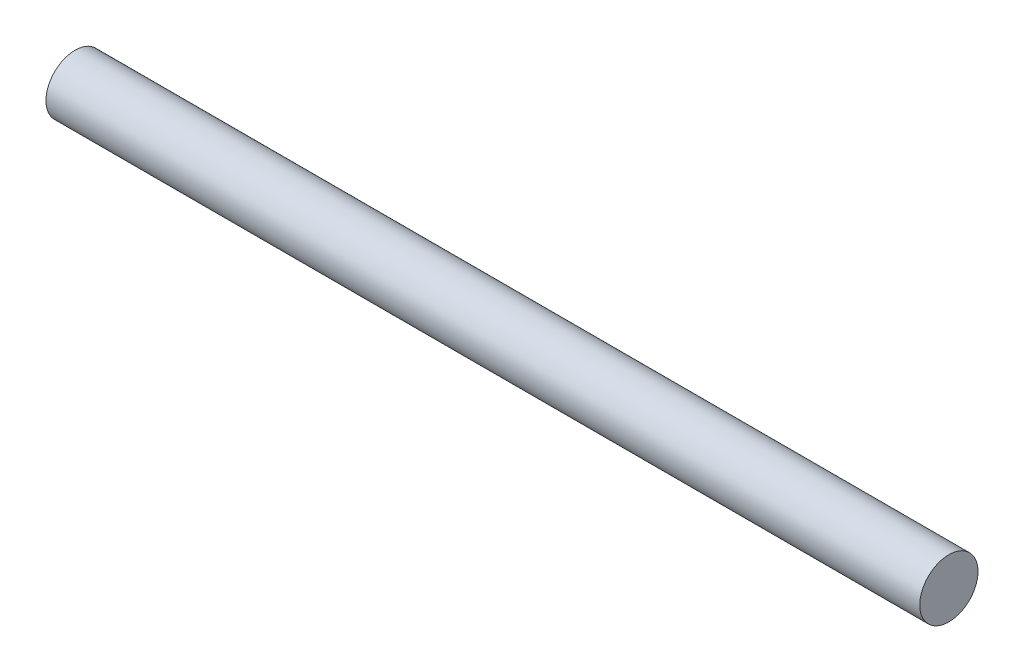
SolidWorks part; units mm, degrees
ref_plane "Alzado" through (0, 0, 0) normal (0, 0, 1) x (1, 0, 0)
ref_plane "Planta" through (0, 0, 0) normal (0, 1, 0) x (1, 0, 0)
ref_plane "Vista lateral" through (0, 0, 0) normal (1, 0, 0) x (0, 0, -1)
sketch "Croquis1" plane through (0, 0, 0) normal (1, 0, 0) x (0, 0, -1)
  circle A0 centre (0, 0) radius 4
  dimension "D1" = 8
extrude "Saliente-Extruir1" add sketch "Croquis1" along normal blind 120
